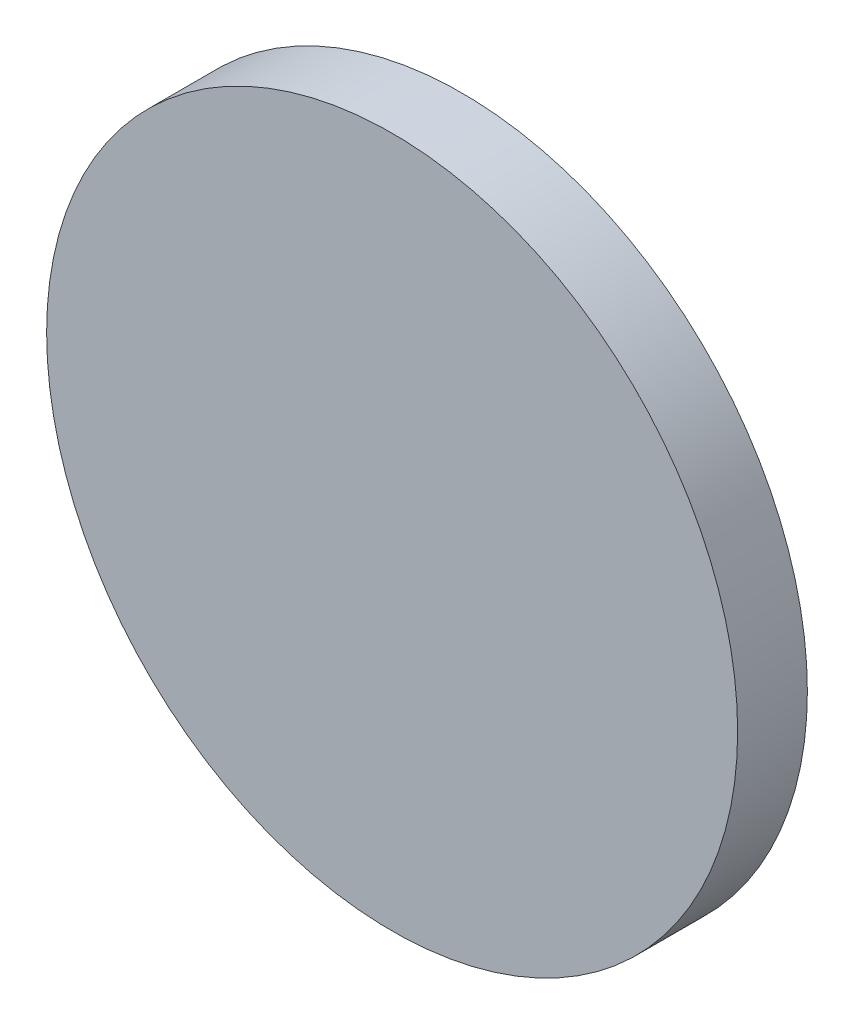
SolidWorks part; units mm, degrees
ref_plane "Front Plane" through (0, 0, 0) normal (0, 0, 1) x (1, 0, 0)
ref_plane "Top Plane" through (0, 0, 0) normal (0, 1, 0) x (1, 0, 0)
ref_plane "Right Plane" through (0, 0, 0) normal (1, 0, 0) x (0, 0, -1)
sketch "Sketch1" plane through (0, 0, 0) normal (0, 0, 1) x (1, 0, 0)
  circle A0 centre (0, 0) radius 28.321
  dimension "D1" = 56.642
extrude "Boss-Extrude1" add sketch "Sketch1" along normal blind 5.715
